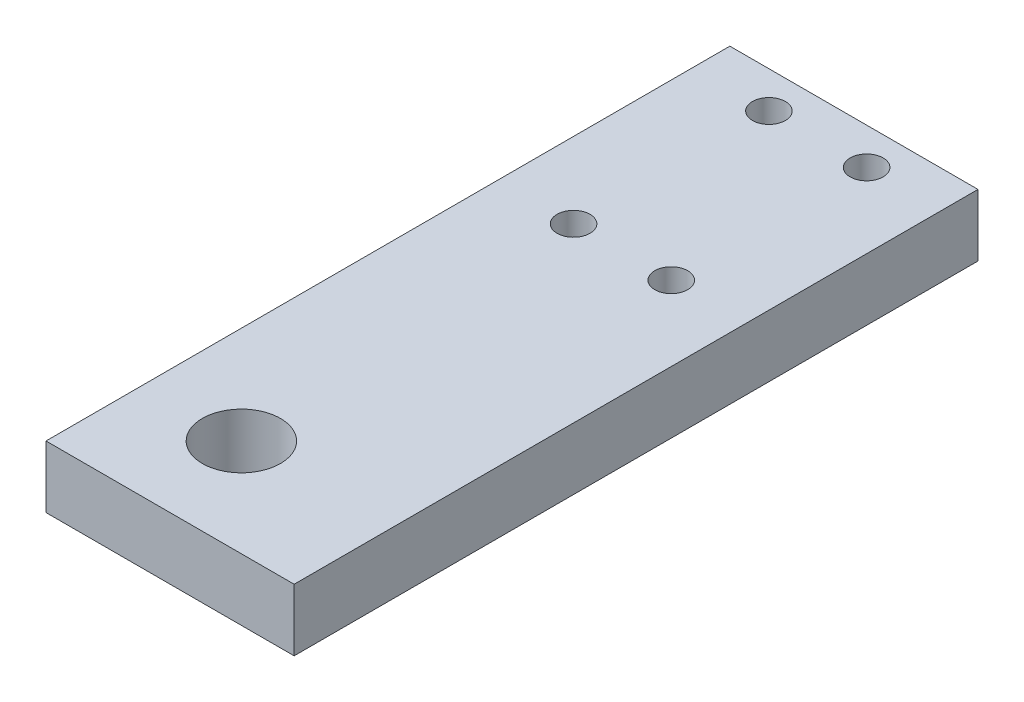
SolidWorks part; units mm, degrees
ref_plane "Front Plane" through (0, 0, 0) normal (0, 0, 1) x (1, 0, 0)
ref_plane "Top Plane" through (0, 0, 0) normal (0, 1, 0) x (1, 0, 0)
ref_plane "Right Plane" through (0, 0, 0) normal (1, 0, 0) x (0, 0, -1)
sketch "Sketch2" plane through (0, 0, 0) normal (0, 1, 0) x (1, 0, 0)
  line L1 (0, 0) -> (101.6, 0)
  line L2 (0, 0) -> (0, 280)
  line L3 (0, 280) -> (101.6, 280)
  line L4 (101.6, 0) -> (101.6, 280)
  dimension "D1" = 101.6
  dimension "D2" = 280
extrude "Boss-Extrude1" add sketch "Sketch2" along normal blind 25.4
sketch "Sketch3" plane through (0, 25.4, 0) normal (0, 1, 0) x (1, 0, 0)
  line L1 (0, 280) -> (51, 280)
  line L2 (0, 280) -> (0, 225)
  line L3 (0, 225) -> (51, 225)
  line L4 (51, 280) -> (51, 225)
  line L5 (31, 185) -> (71, 185)
  line L6 (31, 185) -> (31, 265)
  line L7 (31, 265) -> (71, 265)
  line L8 (71, 185) -> (71, 265)
  line L9 (31, 185) -> (71, 265) construction
  line L10 (31, 265) -> (71, 185) construction
  circle A0 centre (71, 265) radius 6.75
  circle A1 centre (31, 265) radius 6.75
  circle A2 centre (31, 185) radius 6.75
  circle A3 centre (71, 185) radius 6.75
  dimension "D1" = 51
  dimension "D2" = 55
  dimension "D3" = 40
  dimension "D4" = 80
extrude "Cut-Extrude1" cut sketch "Sketch3" against normal blind 25.4 contours A1 | A0 | A3 | A2
sketch "Sketch4" plane through (0, 25.4, 0) normal (0, 1, 0) x (1, 0, 0)
  line L1 (0, 280) -> (40, 280)
  line L2 (0, 280) -> (0, 40)
  line L3 (0, 40) -> (40, 40)
  line L4 (40, 280) -> (40, 40)
  circle A0 centre (40, 40) radius 16
  dimension "D1" = 240
  dimension "D2" = 40
extrude "Cut-Extrude2" cut sketch "Sketch4" against normal blind 25.4 contours A0
